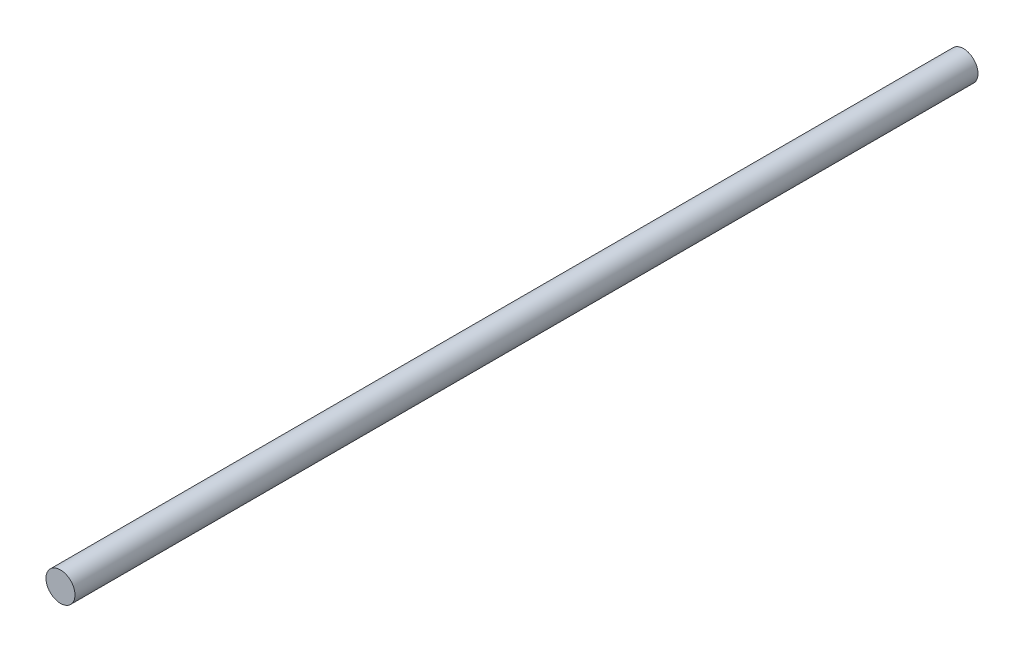
SolidWorks part; units mm, degrees
ref_plane "Front Plane" through (0, 0, 0) normal (0, 0, 1) x (1, 0, 0)
ref_plane "Top Plane" through (0, 0, 0) normal (0, 1, 0) x (1, 0, 0)
ref_plane "Right Plane" through (0, 0, 0) normal (1, 0, 0) x (0, 0, -1)
sketch "Sketch1" plane through (0, 0, 0) normal (0, 0, 1) x (1, 0, 0)
  circle A0 centre (0, 0) radius 1.632
  dimension "D1" = 3.2639
extrude "Boss-Extrude1" add sketch "Sketch1" along normal blind 101.6
